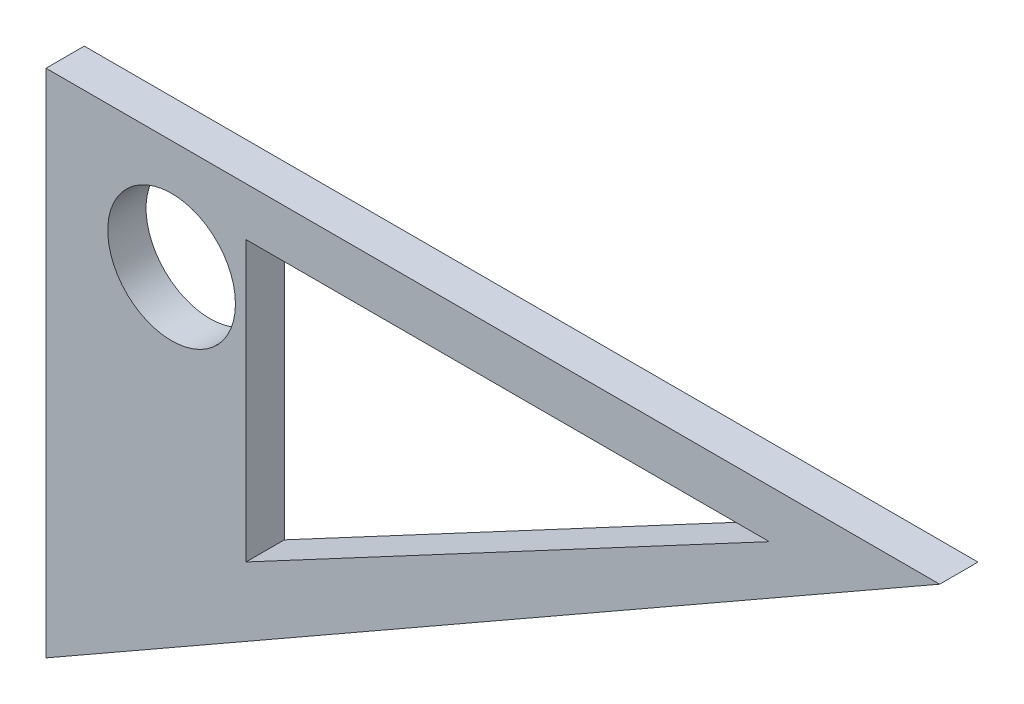
SolidWorks part; units mm, degrees
ref_plane "前视基准面" through (0, 0, 0) normal (0, 0, 1) x (1, 0, 0)
ref_plane "上视基准面" through (0, 0, 0) normal (0, 1, 0) x (1, 0, 0)
ref_plane "右视基准面" through (0, 0, 0) normal (1, 0, 0) x (0, 0, -1)
sketch "草图1" plane through (0, 0, 0) normal (0, 0, 1) x (1, 0, 0)
  line L0 (-9.838, 8.5705) -> (60.162, 8.5705)
  line L1 (5.8319, 4.7822) -> (5.8319, -17.0867)
  line L2 (-9.838, -31.4295) -> (-9.838, 8.5705)
  line L3 (-9.838, -31.4295) -> (60.162, 8.5705)
  line L4 (5.8319, -17.0867) -> (46.8146, 4.7822)
  line L5 (46.8146, 4.7822) -> (5.8319, 4.7822)
  circle A0 centre (0, 0) radius 5
  dimension "D1" = 40
  dimension "D2" = 70
extrude "凸台-拉伸1" add sketch "草图1" along normal blind 3
